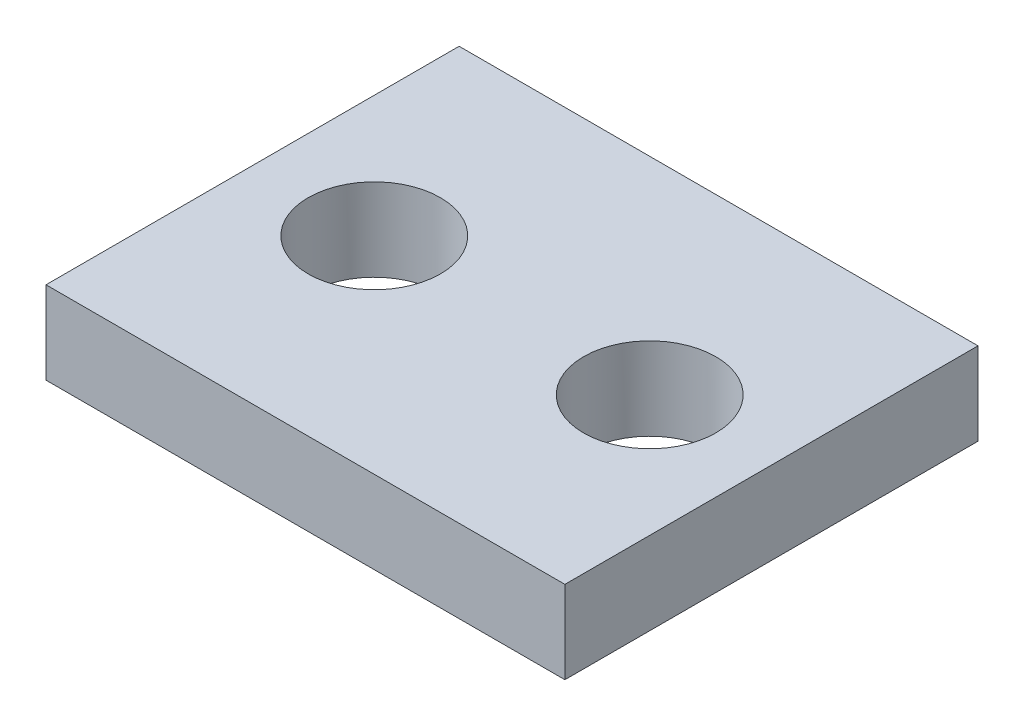
SolidWorks part; units mm, degrees
ref_plane "Front Plane" through (0, 0, 0) normal (0, 0, 1) x (1, 0, 0)
ref_plane "Top Plane" through (0, 0, 0) normal (0, 1, 0) x (1, 0, 0)
ref_plane "Right Plane" through (0, 0, 0) normal (1, 0, 0) x (0, 0, -1)
sketch "Sketch1" plane through (0, 0, 0) normal (0, 1, 0) x (1, 0, 0)
  line L1 (-9.42, -7.5) -> (9.42, -7.5)
  line L2 (-9.42, -7.5) -> (-9.42, 7.5)
  line L3 (-9.42, 7.5) -> (9.42, 7.5)
  line L4 (9.42, -7.5) -> (9.42, 7.5)
  line L5 (-9.42, -7.5) -> (9.42, 7.5) construction
  line L6 (-9.42, 7.5) -> (9.42, -7.5) construction
  point P0 (0, 0)
  dimension "D1" = 18.84
  dimension "D2" = 15
extrude "Boss-Extrude1" add sketch "Sketch1" along normal blind 3
sketch "Sketch2" plane through (0, 3, 0) normal (0, 1, 0) x (1, 0, 0)
  circle A0 centre (-5, 0) radius 2.4
  dimension "D2" = 4.8
  dimension "D1" = 5
extrude "Cut-Extrude1" cut sketch "Sketch2" against normal through all both and the other way through all
mirror "Mirror1" about plane through (0, 0, 0) normal (1, 0, 0) of "Cut-Extrude1"
